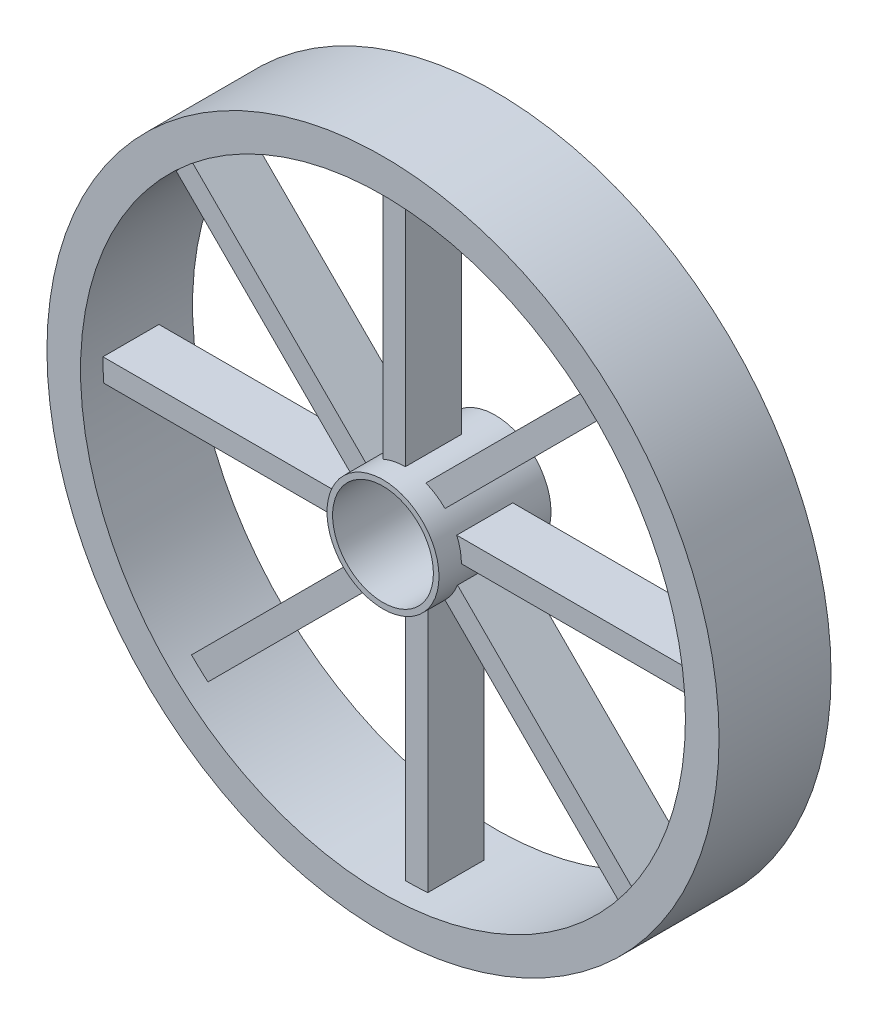
SolidWorks part; units mm, degrees
material "ABS"
ref_plane "Front Plane" through (0, 0, 0) normal (0, 0, 1) x (1, 0, 0)
ref_plane "Top Plane" through (0, 0, 0) normal (0, 1, 0) x (1, 0, 0)
ref_plane "Right Plane" through (0, 0, 0) normal (1, 0, 0) x (0, 0, -1)
sketch "Sketch2" plane through (0, 0, 0) normal (0, 0, 1) x (1, 0, 0)
  circle A0 centre (0, 0) radius 30
  circle A1 centre (0, 0) radius 27
  circle A2 centre (0, 0) radius 4.5
  circle A3 centre (0, 0) radius 5
  dimension "D1" = 60
  dimension "D2" = 3
  dimension "D3" = 10
  dimension "D4" = 9
extrude "Boss-Extrude1" add sketch "Sketch2" along normal blind 10 contours A0 A1 | A3 A2
ref_plane "Plane2" through (-18, 0, 0) normal (1, 0, 0) x (0, 0, -1)
sketch "Sketch4" plane through (-18, 0, 0) normal (1, 0, 0) x (0, 0, -1)
  line L0 (0, 30) -> (-10, 30) construction
  line L1 (-3, 0) -> (-8, 0)
  line L2 (-3, 0) -> (-3, -2)
  line L3 (-3, -2) -> (-8, -2)
  line L4 (-8, 0) -> (-8, -2)
  line L5 (-3, 0) -> (-8, -2) construction
  line L6 (-3, -2) -> (-8, 0) construction
  line L7 (0, -4.5) -> (0, 4.5) construction
  point P0 (-5.5, -1)
  dimension "D1" = 5
  dimension "D2" = 2
  dimension "D3" = 30
  dimension "D4" = 3
extrude "Boss-Extrude2" add sketch "Sketch4" along normal up to next and the other way up to next
pattern_circular "CirPattern1" count 8 every 45 about axis through (0, 0, 0) along (0, 0, 1) of "Boss-Extrude2"
